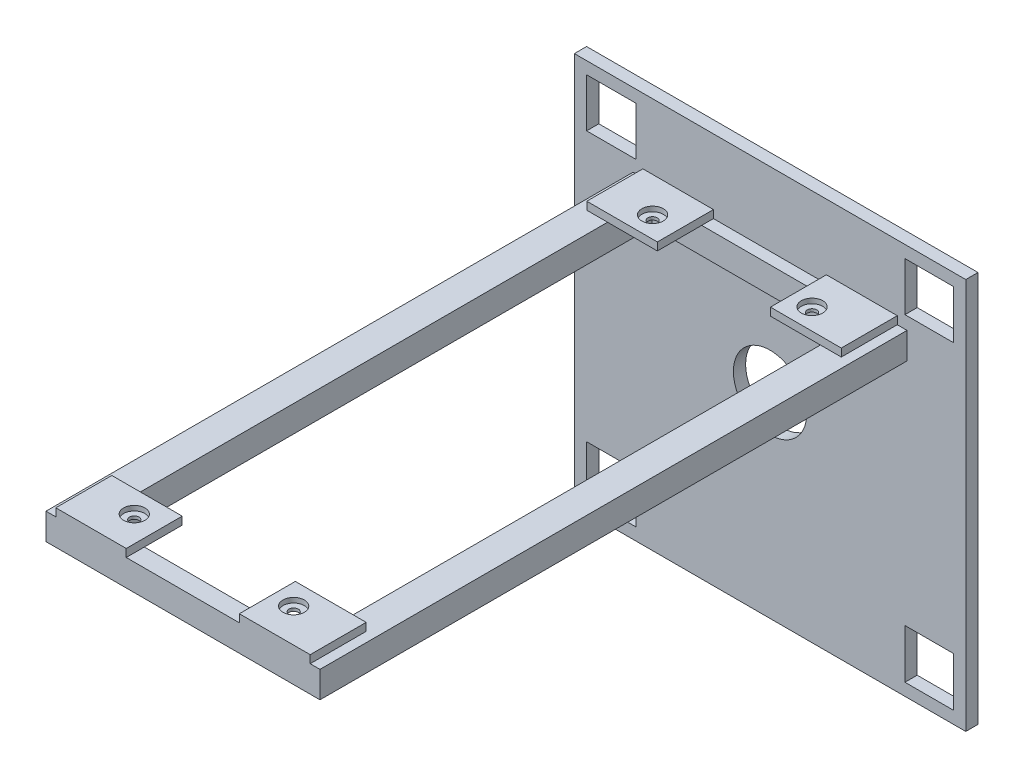
SolidWorks part; units mm, degrees
ref_plane "Front Plane" through (0, 0, 0) normal (0, 0, 1) x (1, 0, 0)
ref_plane "Top Plane" through (0, 0, 0) normal (0, 1, 0) x (1, 0, 0)
ref_plane "Right Plane" through (0, 0, 0) normal (1, 0, 0) x (0, 0, -1)
sketch "Sketch1" plane through (0, 0, 0) normal (0, 0, 1) x (1, 0, 0)
  line L1 (103.2829, -37.7023) -> (1.6829, -37.7023)
  line L2 (103.2829, -37.7023) -> (103.2829, 63.8977)
  line L3 (103.2829, 63.8977) -> (1.6829, 63.8977)
  line L4 (1.6829, -37.7023) -> (1.6829, 63.8977)
  dimension "D1" = 101.6
  dimension "D2" = 101.6
extrude "Boss-Extrude1" add sketch "Sketch1" along normal blind 3.175
sketch "Sketch19" plane through (0, 0, 3.175) normal (0, 0, 1) x (1, 0, 0)
  line L0 (103.2829, 63.8977) -> (1.6829, 63.8977) construction
  line L1 (4.8579, 60.7227) -> (17.6171, 60.7227)
  line L2 (4.8579, 60.7227) -> (4.8579, 48.1127)
  line L3 (4.8579, 48.1127) -> (17.6171, 48.1127)
  line L4 (17.6171, 60.7227) -> (17.6171, 48.1127)
  line L5 (1.6829, 63.8977) -> (1.6829, -37.7023) construction
  line L6 (103.2829, -37.7023) -> (103.2829, 63.8977) construction
  line L7 (100.1079, -34.5273) -> (87.4979, -34.5273)
  line L8 (100.1079, -34.5273) -> (100.1079, -21.7681)
  line L9 (100.1079, -21.7681) -> (87.4979, -21.7681)
  line L10 (87.4979, -34.5273) -> (87.4979, -21.7681)
  line L11 (1.6829, -37.7023) -> (103.2829, -37.7023) construction
  line L13 (100.1079, 60.7227) -> (87.4979, 60.7227)
  line L14 (100.1079, 60.7227) -> (100.1079, 48.1127)
  line L15 (100.1079, 48.1127) -> (87.4979, 48.1127)
  line L16 (87.4979, 60.7227) -> (87.4979, 48.1127)
  line L17 (4.8579, -34.5273) -> (17.6171, -34.5273)
  line L18 (4.8579, -34.5273) -> (4.8579, -21.7681)
  line L19 (4.8579, -21.7681) -> (17.6171, -21.7681)
  line L20 (17.6171, -34.5273) -> (17.6171, -21.7681)
  dimension "D1" = 3.175
  dimension "D2" = 3.175
  dimension "D3" = 3.175
  dimension "D4" = 3.175
extrude "Cut-Extrude1" cut sketch "Sketch19" against normal blind 3.175
sketch "Sketch20" plane through (0, 0, 0) normal (0, 0, -1) x (-1, 0, 0)
  line L0 (-103.2829, 13.0977) -> (-1.6829, 13.0977) construction
  line L1 (-103.2829, -37.7023) -> (-103.2829, 63.8977) construction
  line L2 (-1.6829, 63.8977) -> (-1.6829, -37.7023) construction
hole_wizard "3/4 (0.75) Diameter Hole1" positions "Sketch26" profile "Sketch27" hole size "3/4" standard "ANSI Inch" end condition through all
sketch "Sketch26" plane through (0, 0, 0) normal (0, 0, -1) x (-1, 0, 0)
  line L0 (-103.2829, 13.0977) -> (-1.6829, 13.0977) construction
  point P0 (-52.4829, 13.0977)
sketch "Sketch27" plane through (52.4829, 13.0977, 0) normal (1, 0, 0) x (0, 1, 0)
  line L0 (0, 0) -> (0, 3.175)
  line L1 (0, 3.175) -> (9.525, 3.175)
  line L2 (9.525, 3.175) -> (9.525, 0)
  line L5 (9.525, 0) -> (0, 0)
  line L11 (0, -6.35) -> (0, 107.95) construction
  dimension "Thru Hole Dia." = 19.05
  dimension "Thru Hole Depth" = 3.175
ref_plane "Plane1" through (0, 0, 3.175) normal (0, 0, 1) x (1, 0, 0)
sketch "Sketch29" plane through (0, 0, 3.175) normal (0, 0, 1) x (1, 0, 0)
  line L5 (88.043, 37.9897) -> (16.923, 37.9897)
  line L6 (88.043, 37.9897) -> (88.043, 44.8477)
  line L7 (88.043, 44.8477) -> (16.923, 44.8477)
  line L8 (16.923, 37.9897) -> (16.923, 44.8477)
  line L9 (103.2829, 63.8977) -> (1.6829, 63.8977) construction
  dimension "D1" = 71.12
  dimension "D2" = 0
  dimension "D3" = 19.05
extrude "Boss-Extrude11" add sketch "Sketch29" along normal blind 3.048
sketch "Sketch30" plane through (0, 0, 6.223) normal (0, 0, 1) x (1, 0, 0)
  line L0 (88.043, 44.8477) -> (16.923, 44.8477) construction
  line L1 (88.043, 37.9897) -> (80.0928, 37.9897)
  line L2 (88.043, 37.9897) -> (88.043, 44.8477)
  line L3 (88.043, 44.8477) -> (80.0928, 44.8477)
  line L4 (80.0928, 37.9897) -> (80.0928, 44.8477)
  line L6 (16.923, 37.9897) -> (24.8544, 37.9897)
  line L7 (16.923, 37.9897) -> (16.923, 44.8477)
  line L8 (16.923, 44.8477) -> (24.8544, 44.8477)
  line L9 (24.8544, 37.9897) -> (24.8544, 44.8477)
extrude "Boss-Extrude12" add sketch "Sketch30" along normal blind 149.352
sketch "Sketch31" plane through (80.0928, 0, 0) normal (-1, 0, 0) x (0, 0, 1)
  line L5 (155.575, 37.9897) -> (6.223, 37.9897) construction
  line L6 (155.575, 44.8477) -> (150.8715, 44.8477)
  line L7 (155.575, 44.8477) -> (155.575, 37.9897)
  line L8 (155.575, 37.9897) -> (150.8715, 37.9897)
  line L9 (150.8715, 44.8477) -> (150.8715, 37.9897)
extrude "Boss-Extrude13" add sketch "Sketch31" along normal blind 55.88
sketch "Sketch32" plane through (0, 44.8477, 0) normal (0, 1, 0) x (1, 0, 0)
  line L0 (88.043, -155.575) -> (16.923, -155.575) construction
  line L1 (85.503, -155.575) -> (67.1066, -155.575)
  line L2 (85.503, -155.575) -> (85.503, -141.0412)
  line L3 (85.503, -141.0412) -> (67.1066, -141.0412)
  line L4 (67.1066, -155.575) -> (67.1066, -141.0412)
  line L5 (16.923, -155.575) -> (16.923, -3.175) construction
  line L6 (19.463, -155.575) -> (37.751, -155.575)
  line L7 (19.463, -155.575) -> (19.463, -141.0412)
  line L8 (19.463, -141.0412) -> (37.751, -141.0412)
  line L9 (37.751, -155.575) -> (37.751, -141.0412)
  line L10 (88.043, -155.575) -> (88.043, -3.175) construction
  line L11 (88.043, -3.175) -> (16.923, -3.175) construction
  line L12 (85.503, -3.175) -> (67.1066, -3.175)
  line L13 (85.503, -3.175) -> (85.503, -17.7088)
  line L14 (85.503, -17.7088) -> (67.1066, -17.7088)
  line L15 (67.1066, -3.175) -> (67.1066, -17.7088)
  line L17 (19.463, -3.175) -> (37.7801, -3.175)
  line L18 (19.463, -3.175) -> (19.463, -17.734)
  line L19 (19.463, -17.734) -> (37.7801, -17.734)
  line L20 (37.7801, -3.175) -> (37.7801, -17.734)
  point P24 (0, 0)
  dimension "D1" = 2.54
  dimension "D2" = 2.54
  dimension "D3" = 18.288
  dimension "D4" = 2.54
  dimension "D5" = 2.54
extrude "Boss-Extrude14" add sketch "Sketch32" along normal blind 2.032
hole_wizard "CBORE for #2 Binding Head Machine Screw1" positions "Sketch36" profile "Sketch37" counterbore size "#2" standard "ANSI Inch" end condition through all
sketch "Sketch36" plane through (0, 46.8797, 0) normal (0, 1, 0) x (1, 0, 0)
  point P0 (31.0719, -12.2575)
  point P2 (72.4516, -12.2575)
  point P4 (72.4516, -146.8117)
  point P6 (31.0719, -146.8117)
  point P20 (0, 0)
  point P21 (30.9565, -146.8117)
  point P22 (72.4516, -146.8117)
  point P23 (31.0719, -146.8117)
sketch "Sketch37" plane through (31.0719, 46.8797, 12.2575) normal (1, 0, 0) x (0, 0, 1)
  line L0 (0, 0) -> (0, 84.582)
  line L1 (0, 84.582) -> (1.2192, 84.582)
  line L3 (1.2192, 84.582) -> (1.2192, 1.27)
  line L4 (1.2192, 1.27) -> (2.7788, 1.27)
  line L5 (2.7788, 1.27) -> (2.7788, 0)
  line L7 (2.7788, 0) -> (0, 0)
  line L11 (0, -6.35) -> (0, 107.95) construction
  dimension "Thru Hole Dia." = 2.4384
  dimension "Thru Hole Depth" = 84.582
  dimension "C'Bore Dia." = 5.5575
  dimension "C'Bore Depth" = 1.27
